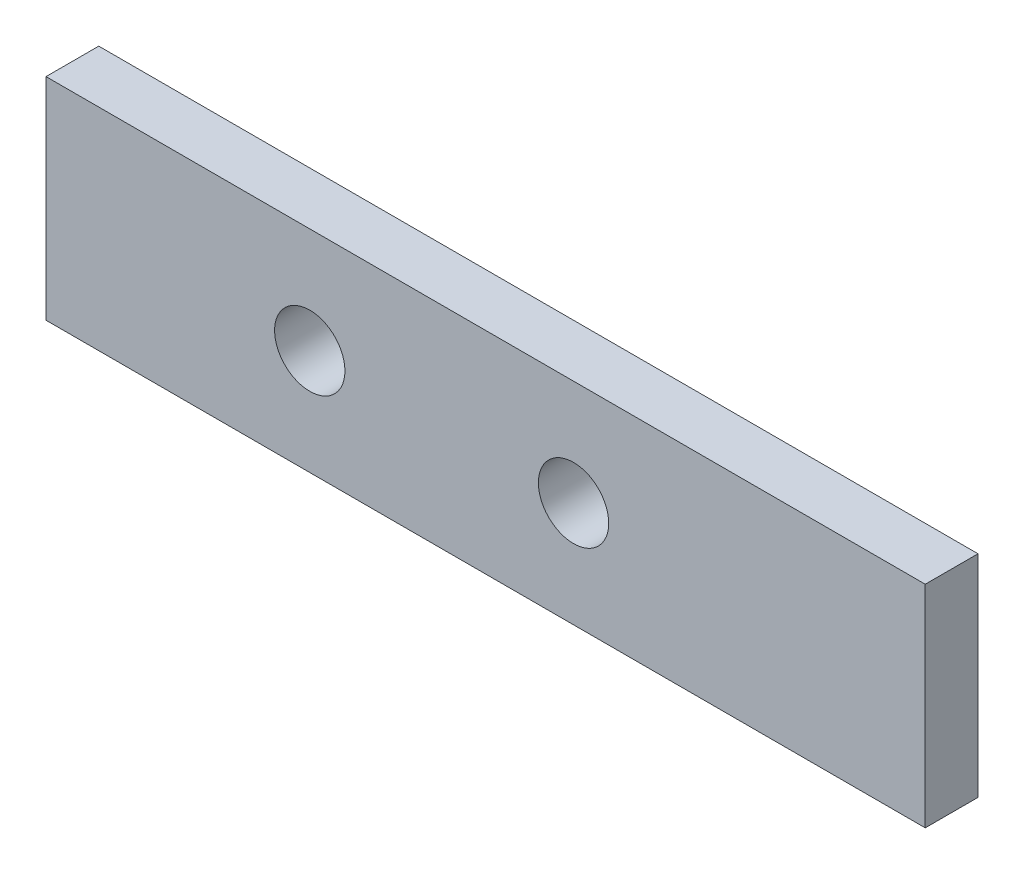
SolidWorks part; units mm, degrees
material "1.0037 (S235JR)"
ref_plane "Plan de face" through (0, 0, 0) normal (0, 0, 1) x (1, 0, 0)
ref_plane "Plan de dessus" through (0, 0, 0) normal (0, 1, 0) x (1, 0, 0)
ref_plane "Plan de droite" through (0, 0, 0) normal (1, 0, 0) x (0, 0, -1)
sketch "Esquisse1" plane through (0, 0, 0) normal (0, 0, 1) x (1, 0, 0)
  line L0 (0, 0) -> (250, 0)
other "Elément mécano-soudé1"
ref_plane "Plan1" through (0, 0, 0) normal (1, 0, 0) x (0, 1, 0)
sketch "plat" plane through (0, 0, 0) normal (1, 0, 0) x (0, 1, 0)
  line L0 (-30, 0) -> (30, 0) construction
  line L1 (-30, 7.5) -> (30, 7.5)
  line L2 (-30, 7.5) -> (-30, -7.5)
  line L3 (-30, -7.5) -> (30, -7.5)
  line L4 (30, 7.5) -> (30, -7.5)
  line L5 (0, 7.5) -> (0, -7.5) construction
  point P8 (0, 0)
  dimension "B" = 60
  dimension "A" = 15
sketch "Esquisse2" plane through (0, 0, 7.5) normal (0, 0, 1) x (1, 0, 0)
  line L0 (0, 0) -> (250, 0) construction
  line L2 (0, 30) -> (0, -30) construction
  circle A0 centre (150, 0) radius 10
  circle A1 centre (75, 0) radius 10
extrude "Enlèv. mat.-Extru.1" cut sketch "Esquisse2" against normal through all
equation "\"D3@Esquisse2\"=\"D2@Esquisse2\""
